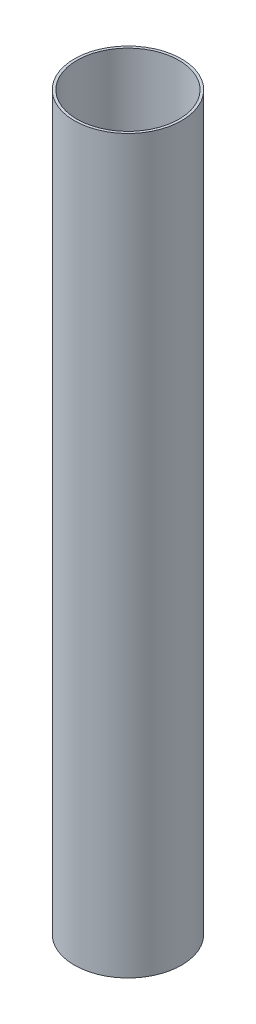
SolidWorks part; units mm, degrees
ref_plane "Front Plane" through (0, 0, 0) normal (0, 0, 1) x (1, 0, 0)
ref_plane "Top Plane" through (0, 0, 0) normal (0, 1, 0) x (1, 0, 0)
ref_plane "Right Plane" through (0, 0, 0) normal (1, 0, 0) x (0, 0, -1)
sketch "Sketch1" plane through (0, 0, 0) normal (0, 1, 0) x (1, 0, 0)
  circle A0 centre (0, 0) radius 40.005
  dimension "D1" = 80.01
extrude "Boss-Extrude1" add sketch "Sketch1" along normal blind 546.1
sketch "Sketch2" plane through (0, 546.1, 0) normal (0, 1, 0) x (1, 0, 0)
  circle A0 centre (0, 0) radius 38.1
  dimension "D1" = 76.2
extrude "Cut-Extrude1" cut sketch "Sketch2" against normal blind 546.1
equation "\"ODia\"= 3.15in"
equation "\"IDia\"= 3in"
equation "\"Length\"= 21.5in"
equation "\"Thick\"= .075in"
